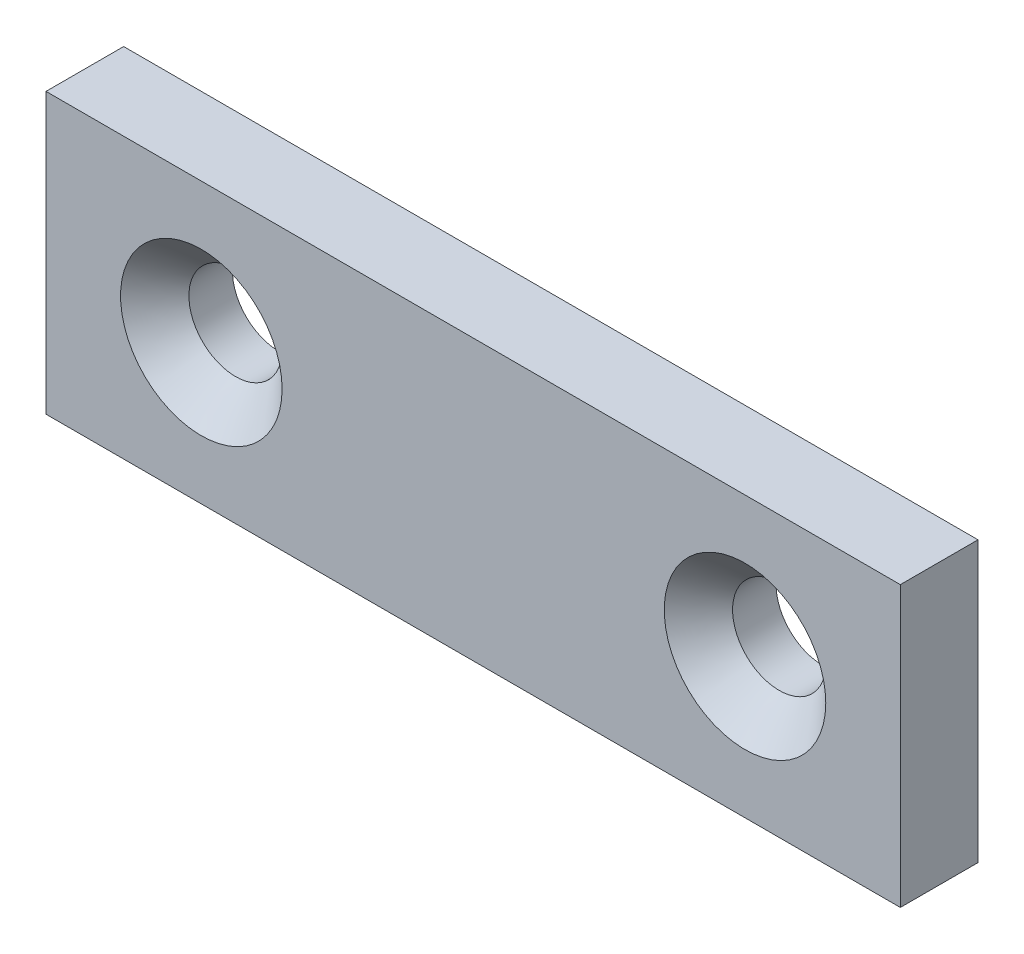
SolidWorks part; units mm, degrees
material "Plain Carbon Steel"
ref_plane "Front Plane" through (0, 0, 0) normal (0, 0, 1) x (1, 0, 0)
ref_plane "Top Plane" through (0, 0, 0) normal (0, 1, 0) x (1, 0, 0)
ref_plane "Right Plane" through (0, 0, 0) normal (1, 0, 0) x (0, 0, -1)
sketch "Sketch2" plane through (0, 0, 0) normal (0, 0, 1) x (1, 0, 0)
  line L1 (0, 0) -> (55, 0)
  line L2 (0, 0) -> (0, 18)
  line L3 (0, 18) -> (55, 18)
  line L4 (55, 0) -> (55, 18)
  dimension "D1" = 18
  dimension "D2" = 55
extrude "Boss-Extrude1" add sketch "Sketch2" along normal mid plane 5
hole_wizard "Ø6.0mm Dowel Hole1" positions "3DSketch1" profile "Sketch3" hole size "Ø6.0" standard "ANSI Metric" end condition through all
sketch3d "3DSketch1"
  point P0 (10, 9, 2.5)
  point P2 (45, 9, 2.5)
sketch "Sketch3" plane through (10, 9, 2.5) normal (1, 0, 0) x (0, -1, 0)
  line L0 (0, 0) -> (0, 5)
  line L1 (0, 5) -> (3, 5)
  line L2 (3, 5) -> (3, 2.2)
  line L3 (3, 2.2) -> (5.2, 0)
  line L5 (5.2, 0) -> (0, 0)
  line L6 (-3, 2.2) -> (-5.2, 0) construction
  line L11 (0, -6.35) -> (0, 107.95) construction
  dimension "Thru Hole Dia." = 6
  dimension "Thru Hole Depth" = 5
  dimension "Near C'Sink Dia." = 10.4
  dimension "Near C'Sink Angle" = 90
